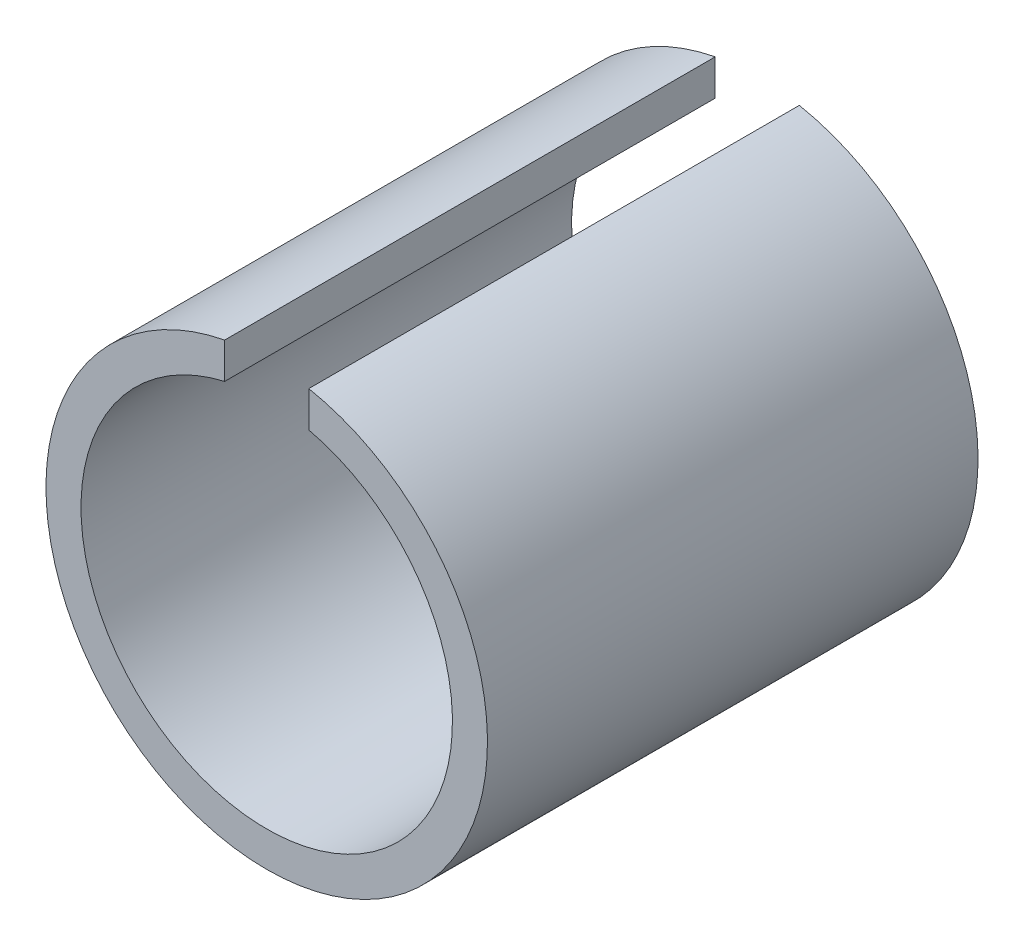
SolidWorks part; units mm, degrees
material "Brass"
ref_plane "Front Plane" through (0, 0, 0) normal (0, 0, 1) x (1, 0, 0)
ref_plane "Top Plane" through (0, 0, 0) normal (0, 1, 0) x (1, 0, 0)
ref_plane "Right Plane" through (0, 0, 0) normal (1, 0, 0) x (0, 0, -1)
sketch "Sketch1" plane through (0, 0, 0) normal (0, 0, 1) x (1, 0, 0)
  line L0 (-0.6, 3.0923) -> (-0.6, 2.5812)
  line L1 (0.6, 3.0923) -> (0.6, 2.5812)
  arc A0 (-0.6, 3.0923) -> (0.6, 3.0923) centre (0, 0) ccw
  arc A1 (-0.6, 2.5812) -> (0.6, 2.5812) centre (0, 0) ccw
  circle A3 centre (0, 0) radius 2.65 construction
  circle A4 centre (0, 0) radius 3.15 construction
  point P4 (3.0124, 0.921)
  point P9 (2.65, 0)
  dimension "D1" = 6.3
  dimension "D3" = 0.6
  dimension "D4" = 1.2
  dimension "D2" = 0.5
extrude "Boss-Extrude1" add sketch "Sketch1" along normal blind 7
